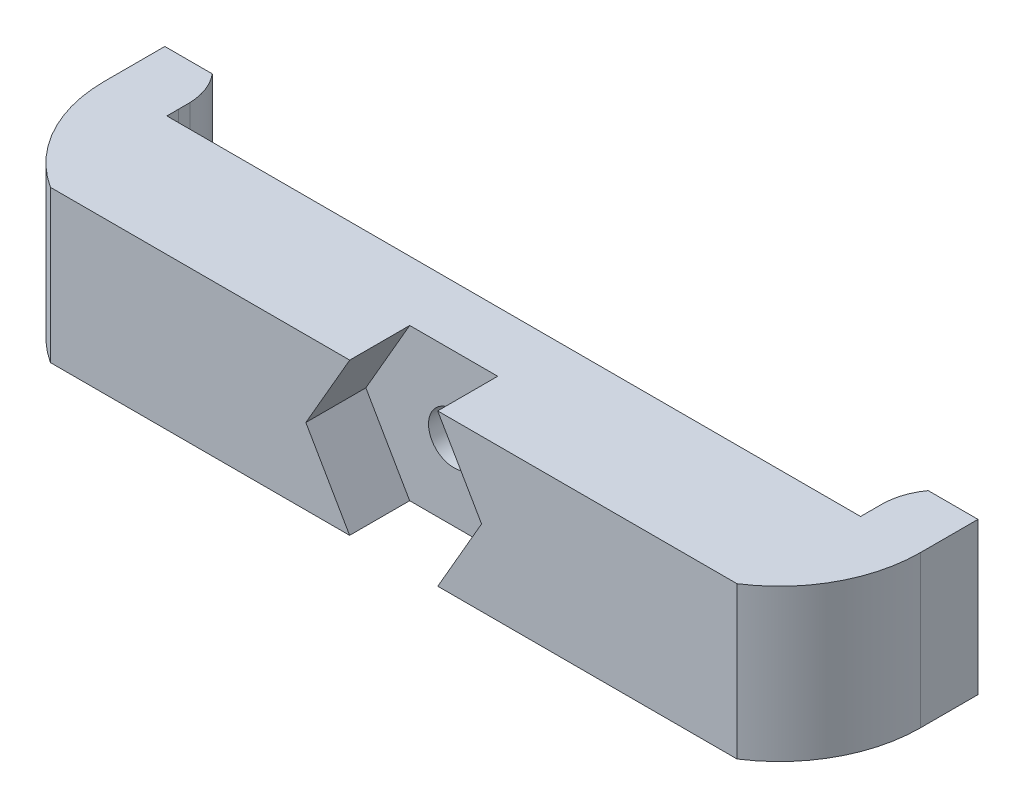
SolidWorks part; units mm, degrees
ref_plane "前视基准面" through (0, 0, 0) normal (0, 0, 1) x (1, 0, 0)
ref_plane "上视基准面" through (0, 0, 0) normal (0, 1, 0) x (1, 0, 0)
ref_plane "右视基准面" through (0, 0, 0) normal (1, 0, 0) x (0, 0, -1)
sketch "草图1" plane through (0, 0, 0) normal (0, 1, 0) x (1, 0, 0)
  line L0 (-28.6, 0) -> (28.6, 0)
  line L1 (-34, 17.2661) -> (-34, 9.892)
  line L2 (-34, 17.2661) -> (-28.9, 15)
  line L3 (28.9, 15) -> (28.9, 10)
  line L4 (28.9, 10) -> (-28.9, 10)
  line L5 (34, 17.2661) -> (34, 9.892)
  line L6 (-28.9, 15) -> (-28.9, 10)
  line L7 (34, 17.2661) -> (28.9, 15)
  arc A3 (-34, 9.892) -> (-28.6, 0) centre (-22.2396, 9.892) ccw
  arc A5 (34, 9.892) -> (28.6, 0) centre (22.2396, 9.892) cw
extrude "凸台-拉伸1" add sketch "草图1" along normal blind 12.65
sketch "草图2" plane through (0, 0, 0) normal (0, 0, 1) x (1, 0, 0)
  line L1 (-7.32, 6.32) -> (-3.66, -0.0193)
  line L2 (-3.66, -0.0193) -> (3.66, -0.0193)
  line L3 (3.66, -0.0193) -> (7.32, 6.32)
  line L4 (7.32, 6.32) -> (3.66, 12.6593)
  line L5 (3.66, 12.6593) -> (-3.66, 12.6593)
  line L6 (-3.66, 12.6593) -> (-7.32, 6.32)
  circle A0 centre (0, 6.32) radius 6 construction
extrude "切除-拉伸1" cut sketch "草图2" against normal blind 5 contours L5 L6 L1 L2 L3 L4
sketch "草图3" plane through (0, 0, -10) normal (0, 0, -1) x (-1, 0, 0)
  circle A0 centre (0, 6.32) radius 4.75
  dimension "D1" = 9.5
extrude "切除-拉伸2" cut sketch "草图3" against normal blind 3
ref_plane "基准面2" through (0, 12.65, 0) normal (0, -1, 0) x (-1, 0, 0)
sketch "草图6" plane through (0, 0, -5) normal (0, 0, 1) x (1, 0, 0)
  circle A0 centre (0, 6.32) radius 2.1
extrude "切除-拉伸5" cut sketch "草图6" against normal blind 10
fillet "圆角3" radius 5 1 edges at (-28.9, 6.325, -15)
fillet "圆角4" radius 5 1 edges at (28.9, 6.325, -15)
fillet "圆角6" radius 1 1 edges at (34, 6.325, -17.2661)
fillet "圆角7" radius 1 1 edges at (-34, 6.325, -17.2661)
sketch "草图7" plane through (0, 0, 0) normal (0, -1, 0) x (1, 0, 0)
  line L1 (28.9034, -10.9422) -> (27.4075, -14.6836)
  line L2 (-28.9034, -10.9422) -> (-27.7112, -14.9305)
  line L3 (-27.7112, -14.9305) -> (-28.9034, -15.7562)
  line L5 (-28.9034, -15.7562) -> (-29.0089, -15.7815)
  line L6 (28.9034, -10.9422) -> (28.9034, -14.6836)
  line L8 (27.4075, -14.6836) -> (28.9034, -17.3433)
  line L9 (28.9034, -14.6836) -> (31.998, -14.6836)
  line L10 (31.998, -14.6836) -> (35.6439, -14.6836)
  line L11 (-28.9034, -10.9422) -> (-28.9034, -14.9305)
  line L12 (-28.9034, -14.9305) -> (-32.1765, -14.9305)
  line L13 (35.6439, -14.6836) -> (36.5005, -19.1876)
  line L14 (36.5005, -19.1876) -> (28.9034, -17.3433)
  line L15 (-32.1765, -14.9305) -> (-36.7207, -14.9305)
  line L16 (-36.7207, -14.9305) -> (-34.951, -20.851)
  line L17 (-34.951, -20.851) -> (-29.0089, -15.7815)
extrude "切除-拉伸6" cut sketch "草图7" against normal blind 15
